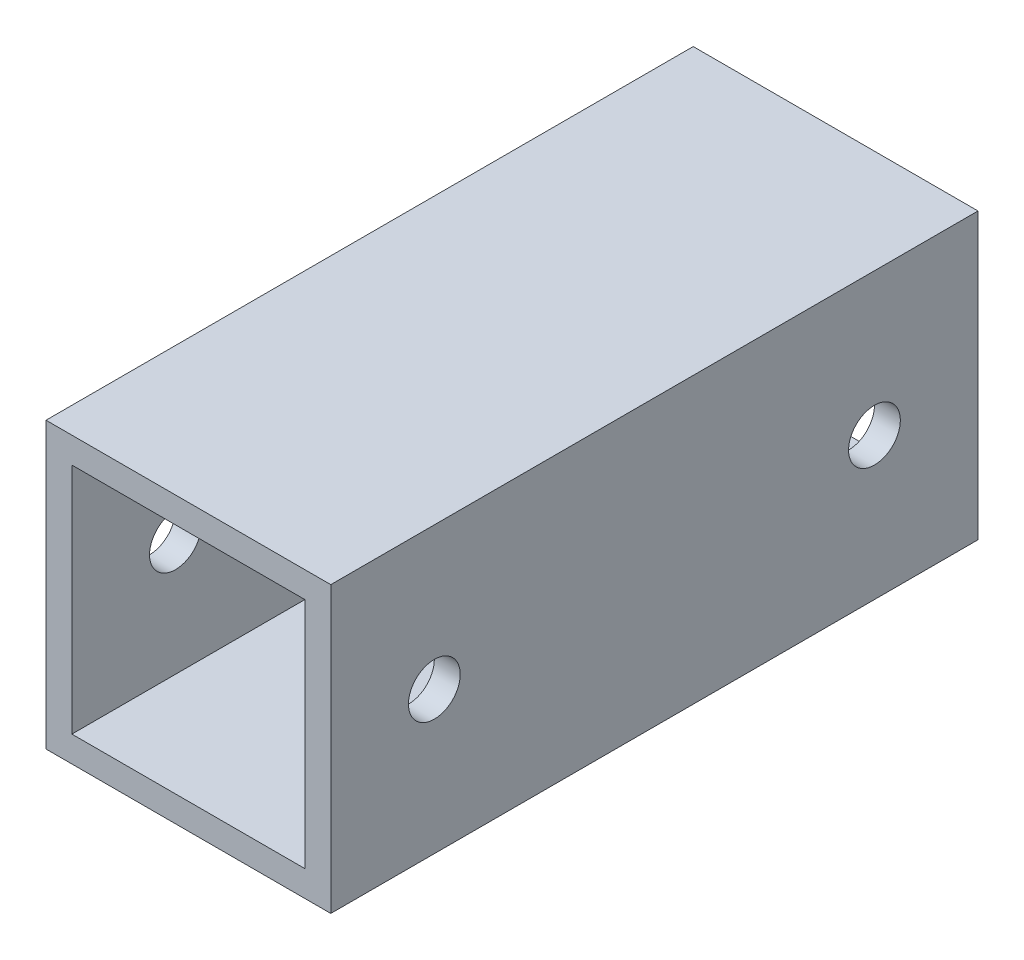
SolidWorks part; units mm, degrees
ref_plane "Front Plane" through (0, 0, 0) normal (0, 0, 1) x (1, 0, 0)
ref_plane "Top Plane" through (0, 0, 0) normal (0, 1, 0) x (1, 0, 0)
ref_plane "Right Plane" through (0, 0, 0) normal (1, 0, 0) x (0, 0, -1)
sketch "Sketch1" plane through (0, 0, 0) normal (0, 0, 1) x (1, 0, 0)
  line L1 (-20, 20) -> (20, 20)
  line L2 (-20, 20) -> (-20, -20)
  line L3 (-20, -20) -> (20, -20)
  line L4 (20, 20) -> (20, -20)
  line L5 (-20, 20) -> (20, -20) construction
  line L6 (-20, -20) -> (20, 20) construction
  point P0 (0, 0)
  dimension "D1" = 40
  dimension "D2" = 40
extrude "Extrude-Thin1" add sketch "Sketch1" along normal mid plane 100 thin thin type mid plane wall 4
sketch "Sketch2" plane through (-22, 0, 0) normal (-1, 0, 0) x (0, 0, 1)
  circle A0 centre (34, 0) radius 4
  circle A1 centre (-34, 0) radius 4
  dimension "D1" = 34
  dimension "D2" = 68
extrude "Cut-Extrude1" cut sketch "Sketch2" against normal through all
